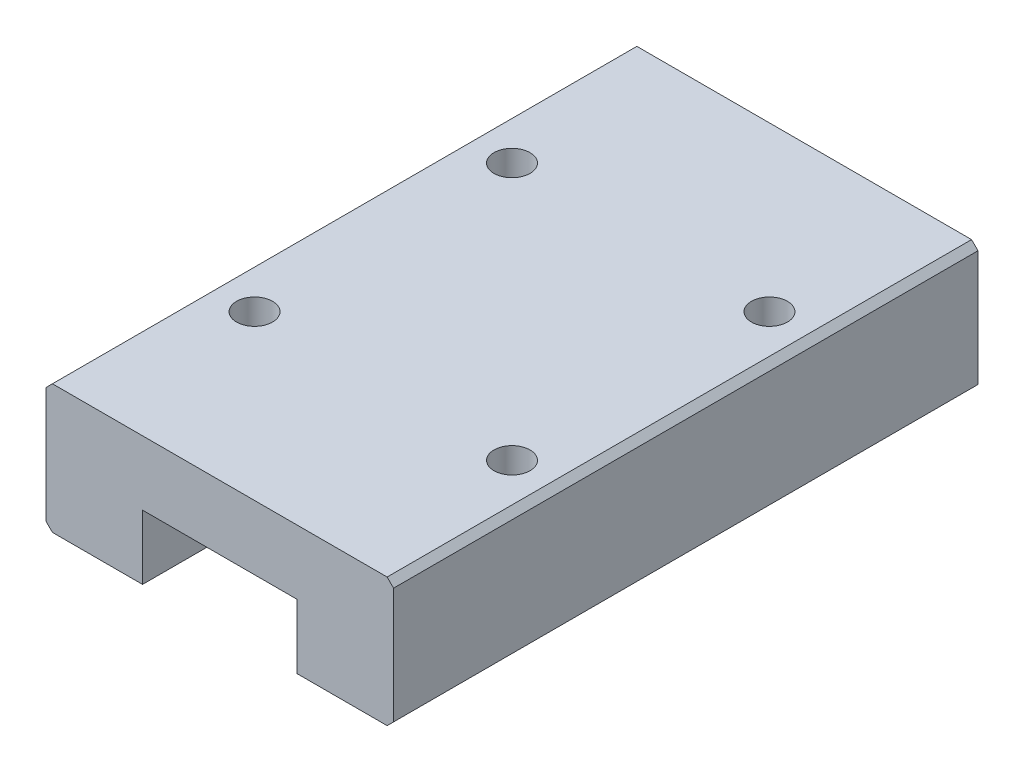
SolidWorks part; units mm, degrees
ref_plane "前视基准面" through (0, 0, 0) normal (0, 0, 1) x (1, 0, 0)
ref_plane "上视基准面" through (0, 0, 0) normal (0, 1, 0) x (1, 0, 0)
ref_plane "右视基准面" through (0, 0, 0) normal (1, 0, 0) x (0, 0, -1)
sketch "草图1" plane through (0, 0, 0) normal (0, 0, 1) x (1, 0, 0)
  line L0 (-1.5769, 14.044) -> (24.4231, 14.044)
  line L1 (-2.0769, 13.544) -> (-2.0769, 4.544)
  line L2 (-1.5769, 4.044) -> (5.4231, 4.044)
  line L3 (24.9231, 13.544) -> (24.9231, 4.544)
  line L4 (5.4231, 9.044) -> (5.4231, 4.044)
  line L5 (17.4231, 9.044) -> (17.4231, 4.044)
  line L6 (-2.0769, 13.544) -> (-1.5769, 14.044)
  line L7 (17.4231, 9.044) -> (5.4231, 9.044)
  line L8 (24.4231, 14.044) -> (24.9231, 13.544)
  line L9 (17.4231, 4.044) -> (24.4231, 4.044)
  line L10 (24.9231, 4.544) -> (24.4231, 4.044)
  line L11 (-2.0769, 4.544) -> (-1.5769, 4.044)
  point P0 (-2.0769, 14.044)
  point P1 (24.9231, 14.044)
  point P3 (24.9231, 4.044)
  point P4 (-2.0769, 4.044)
  dimension "D1" = 27
  dimension "D2" = 10
  dimension "D3" = 7.5
  dimension "D4" = 7.5
extrude "凸台-拉伸1" add sketch "草图1" along normal blind 45.4 contours L0 L8 L3 L10 L9 L5 L7 L4 L2 L11 L1 L6
sketch "草图2" plane through (0, 14.044, 0) normal (0, 1, 0) x (1, 0, 0)
  line L0 (11.4231, -38.9) -> (11.4231, -6.5)
  line L3 (-1.4128, -22.7) -> (24.4231, -22.7)
  line L4 (24.4231, -45.4) -> (24.4231, 0) construction
  line L5 (21.4231, -12.7) -> (1.4231, -12.7)
  line L6 (21.4231, -32.7) -> (1.4231, -32.7)
  line L7 (21.4231, -38.9) -> (21.4231, -6.5)
  line L8 (1.4231, -38.9) -> (1.4231, -6.5)
  line L9 (21.4231, -38.9) -> (1.4231, -38.9)
  line L10 (1.4231, -6.5) -> (21.4231, -6.5)
  dimension "D1" = 10
  dimension "D2" = 10
  dimension "D3" = 10
  dimension "D4" = 10
  dimension "D5" = 16.2
  dimension "D6" = 16.2
hole_wizard "孔2" positions "3D草图2" profile "草图4" legacy
sketch3d "3D草图2"
  point P0 (21.4231, 14.044, 32.7)
  point P3 (21.4231, 14.044, 12.7)
  point P6 (1.4231, 14.044, 12.7)
  point P9 (1.4231, 14.044, 32.7)
sketch "草图4" plane through (21.4231, 14.044, 32.7) normal (1, 0, 0) x (0, 0, 1)
  line L0 (0, 0) -> (0, 3.5)
  line L1 (0, 3.5) -> (1.4, 3.5)
  line L2 (1.4, 3.5) -> (1.4, 0)
  line L3 (1.4, 0) -> (0, 0)
  line L4 (0, 110) -> (0, -10) construction
  dimension "直径" = 2.8
  dimension "深度" = 3.5
